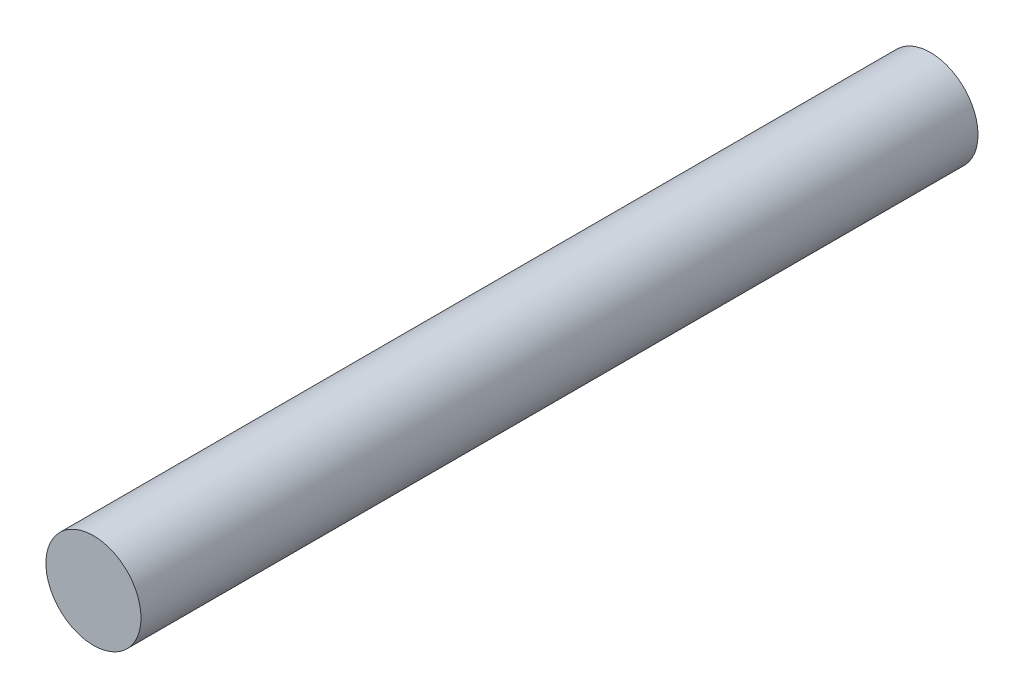
SolidWorks part; units mm, degrees
ref_plane "Front Plane" through (0, 0, 0) normal (0, 0, 1) x (1, 0, 0)
ref_plane "Top Plane" through (0, 0, 0) normal (0, 1, 0) x (1, 0, 0)
ref_plane "Right Plane" through (0, 0, 0) normal (1, 0, 0) x (0, 0, -1)
sketch "Sketch1" plane through (0, 0, 0) normal (0, 0, 1) x (1, 0, 0)
  circle A0 centre (0, 0) radius 1.5875
  dimension "D1" = 3.175
extrude "Boss-Extrude1" add sketch "Sketch1" along normal offset from surface (27.94 mm away) 3.175
